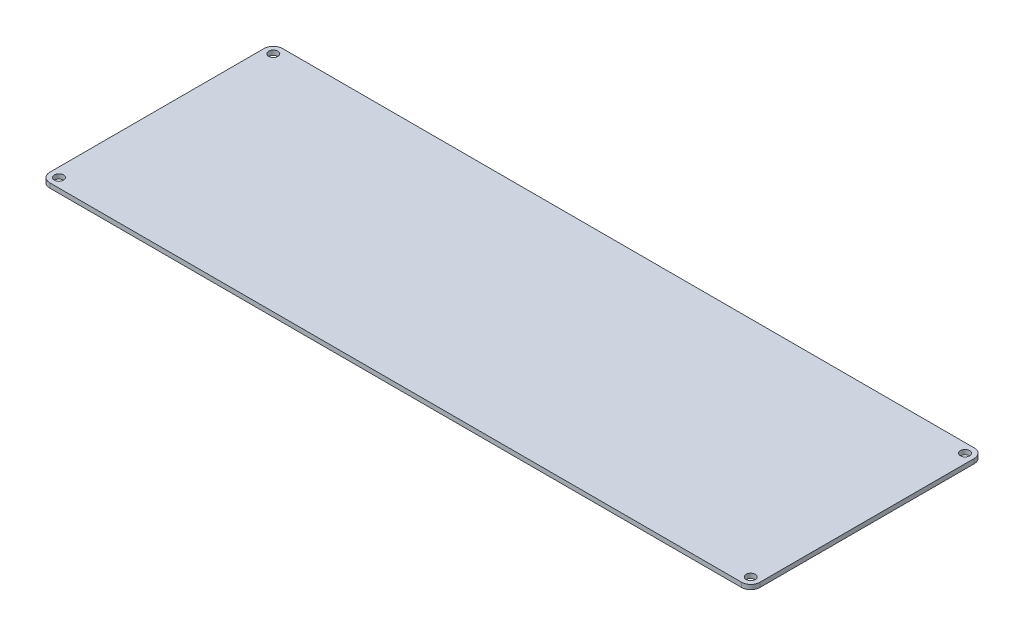
SolidWorks part; units mm, degrees
material "Delrin 2700 NC010, Low Viscosity Acetal Copolymer (SS)"
ref_plane "Front" through (0, 0, 0) normal (0, 0, 1) x (1, 0, 0)
ref_plane "Top" through (0, 0, 0) normal (0, 1, 0) x (1, 0, 0)
ref_plane "Right" through (0, 0, 0) normal (1, 0, 0) x (0, 0, -1)
sketch "Sketch1" plane through (0, 0, 0) normal (0, 1, 0) x (1, 0, 0)
  line L0 (13.7815, 107.0971) -> (20.1315, 107.0971) construction
  line L5 (-25.0185, 160.8971) -> (13.7815, 160.8971) construction
  line L6 (-25.0185, 160.8971) -> (-25.0185, 107.0971) construction
  line L7 (-25.0185, 107.0971) -> (13.7815, 107.0971) construction
  line L8 (13.7815, 160.8971) -> (13.7815, 107.0971) construction
  line L9 (-131.3685, 160.8971) -> (-31.3685, 160.8971) construction
  line L10 (-131.3685, 160.8971) -> (-131.3685, 70.8971) construction
  line L11 (-131.3685, 70.8971) -> (-31.3685, 70.8971) construction
  line L12 (-31.3685, 160.8971) -> (-31.3685, 70.8971) construction
  line L13 (20.1315, 160.8971) -> (58.9315, 160.8971) construction
  line L14 (20.1315, 160.8971) -> (20.1315, 107.0971) construction
  line L15 (20.1315, 107.0971) -> (58.9315, 107.0971) construction
  line L16 (58.9315, 160.8971) -> (58.9315, 107.0971) construction
  line L17 (65.2815, 160.8971) -> (104.0815, 160.8971) construction
  line L18 (65.2815, 160.8971) -> (65.2815, 107.0971) construction
  line L19 (65.2815, 107.0971) -> (104.0815, 107.0971) construction
  line L20 (104.0815, 160.8971) -> (104.0815, 107.0971) construction
  line L21 (58.9315, 107.0971) -> (65.2815, 107.0971) construction
  line L22 (-150.4185, 179.9471) -> (327.6015, 179.9471) construction
  line L27 (-156.7685, 186.2971) -> (333.9515, 186.2971)
  line L28 (-156.7685, 186.2971) -> (-156.7685, 25.5151)
  line L29 (-156.7685, 25.5151) -> (333.9515, 25.5151)
  line L30 (333.9515, 186.2971) -> (333.9515, 25.5151)
  line L31 (327.6015, 179.9471) -> (327.6015, 31.8651) construction
  line L32 (-150.4185, 31.8651) -> (327.6015, 31.8651) construction
  line L33 (-150.4185, 179.9471) -> (-150.4185, 31.8651) construction
  line L34 (-25.0185, 160.8971) -> (-31.3685, 160.8971) construction
  line L35 (104.0815, 160.8971) -> (110.4315, 160.8971) construction
  line L36 (110.4315, 160.8971) -> (308.5515, 160.8971) construction
  line L37 (110.4315, 160.8971) -> (110.4315, 50.9151) construction
  line L38 (110.4315, 50.9151) -> (308.5515, 50.9151) construction
  line L39 (308.5515, 160.8971) -> (308.5515, 50.9151) construction
  circle A0 centre (-150.4185, 179.9471) radius 3.175
  circle A1 centre (-150.4185, 31.8651) radius 3.175
  circle A2 centre (327.6015, 31.8651) radius 3.175
  circle A3 centre (327.6015, 179.9471) radius 3.175
  point P28 (178.5621, 149.4345)
  dimension "D14" = 6.35
  dimension "D2" = 19.05
  dimension "D3" = 38.8
  dimension "D4" = 100
  dimension "D5" = 90
  dimension "D6" = 53.8
  dimension "D7" = 19.05
  dimension "D8" = 19.05
  dimension "D9" = 198.12
  dimension "D10" = 6.35
  dimension "D11" = 19.05
  dimension "D12" = 109.982
  dimension "D13" = 6.35
extrude "Boss-Extrude1" add sketch "Sketch1" against normal blind 3.175 contours L30 L27 L28 L29 A3 A2 A1 A0
fillet "Fillet1" radius 6.35 4 edges at (-156.7685, -1.5875, -186.2971) (-156.7685, -1.5875, -25.5151) (333.9515, -1.5875, -25.5151) (333.9515, -1.5875, -186.2971)
